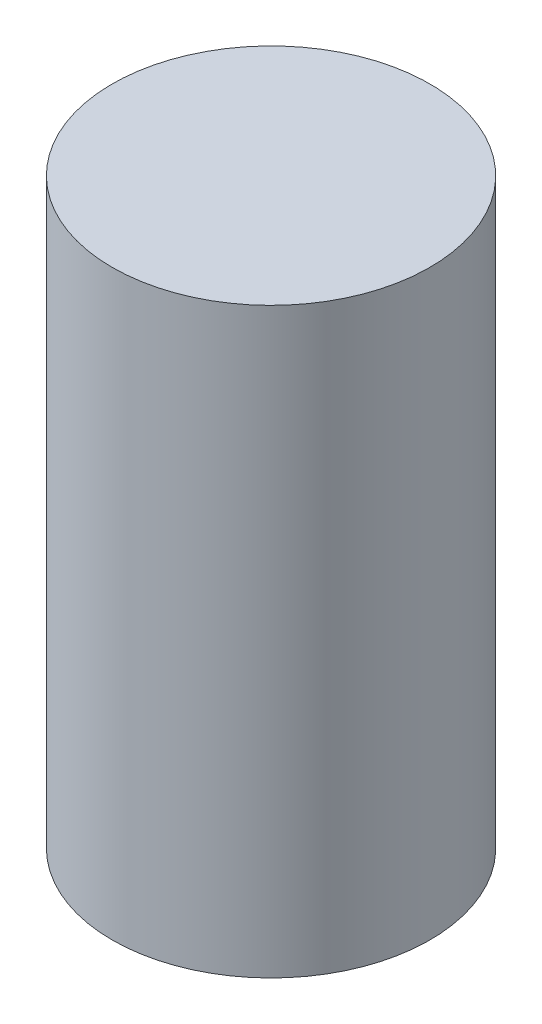
SolidWorks part; units mm, degrees
ref_plane "Front Plane" through (0, 0, 0) normal (0, 0, 1) x (1, 0, 0)
ref_plane "Top Plane" through (0, 0, 0) normal (0, 1, 0) x (1, 0, 0)
ref_plane "Right Plane" through (0, 0, 0) normal (1, 0, 0) x (0, 0, -1)
sketch "Sketch1" plane through (0, 0, 0) normal (0, 1, 0) x (1, 0, 0)
  circle A0 centre (0, 0) radius 9
  dimension "D1" = 18
extrude "Boss-Extrude1" add sketch "Sketch1" along normal blind 33
